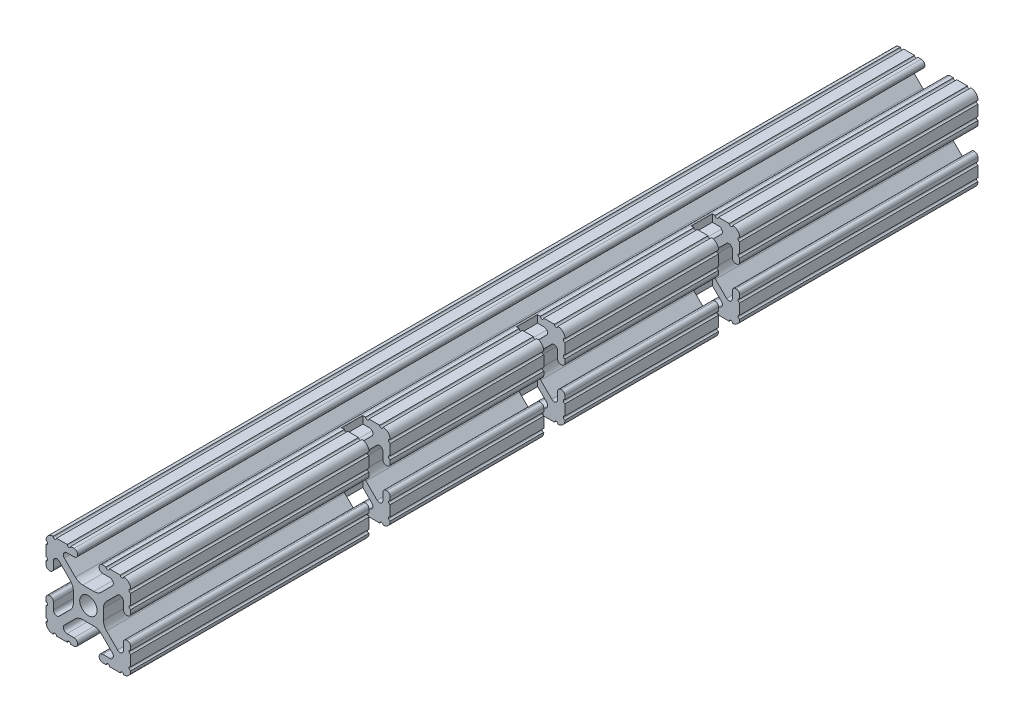
SolidWorks part; units mm, degrees
material "6061-T6 (SS)"
ref_plane "Front" through (0, 0, 0) normal (0, 0, 1) x (1, 0, 0)
ref_plane "Top" through (0, 0, 0) normal (0, 1, 0) x (1, 0, 0)
ref_plane "Right" through (0, 0, 0) normal (1, 0, 0) x (0, 0, -1)
sketch "Sketch1" plane through (0, 0, 0) normal (0, 0, 1) x (1, 0, 0)
  line L0 (-7.5107, 9.4563) -> (7.5107, 9.4563) construction
  line L1 (-7.4968, -9.4098) -> (7.4968, -9.4098) construction
  line L88 (-7.1797, -8.6452) -> (-3.9523, -5.4237)
  line L89 (-1.7093, -4.4958) -> (1.7093, -4.4958)
  line L90 (3.9523, -5.4237) -> (7.1797, -8.6452)
  line L91 (6.4164, -10.4902) -> (4.2875, -10.4902)
  line L92 (3.2385, -11.5392) -> (3.2385, -11.651)
  line L93 (4.2875, -12.7) -> (5.3171, -12.7)
  line L94 (6.3331, -12.7) -> (9.5504, -12.7)
  line L95 (12.7, -9.5504) -> (12.7, -6.3331)
  line L96 (12.7, -5.3171) -> (12.7, -4.2875)
  line L97 (11.651, -3.2385) -> (11.5392, -3.2385)
  line L98 (10.4902, -4.2875) -> (10.4902, -6.4021)
  line L99 (8.7371, -7.1294) -> (5.441, -3.8408)
  line L100 (4.5085, -1.5932) -> (4.5085, 1.5932)
  line L101 (5.441, 3.8408) -> (8.7371, 7.1294)
  line L102 (10.4902, 6.4021) -> (10.4902, 4.2875)
  line L103 (11.5392, 3.2385) -> (11.651, 3.2385)
  line L104 (12.7, 4.2875) -> (12.7, 5.3171)
  line L105 (12.7, 6.3331) -> (12.7, 9.5504)
  line L106 (9.5504, 12.7) -> (6.3331, 12.7)
  line L107 (5.3171, 12.7) -> (4.2875, 12.7)
  line L108 (3.2385, 11.651) -> (3.2385, 11.5392)
  line L109 (4.2875, 10.4902) -> (6.4768, 10.4902)
  line L110 (7.207, 8.7244) -> (3.8983, 5.4232)
  line L111 (1.6558, 4.4958) -> (-1.6558, 4.4958)
  line L112 (-3.8983, 5.4232) -> (-7.207, 8.7244)
  line L113 (-6.4768, 10.4902) -> (-4.2875, 10.4902)
  line L114 (-3.2385, 11.5392) -> (-3.2385, 11.651)
  line L115 (-4.2875, 12.7) -> (-5.3171, 12.7)
  line L116 (-6.3331, 12.7) -> (-9.5504, 12.7)
  line L117 (-12.7, 9.5504) -> (-12.7, 6.3331)
  line L118 (-12.7, 5.3171) -> (-12.7, 4.2875)
  line L119 (-11.651, 3.2385) -> (-11.5392, 3.2385)
  line L120 (-10.4902, 4.2875) -> (-10.4902, 6.4021)
  line L121 (-8.7371, 7.1294) -> (-5.441, 3.8408)
  line L122 (-4.5085, 1.5932) -> (-4.5085, -1.5932)
  line L123 (-5.441, -3.8408) -> (-8.7371, -7.1294)
  line L124 (-10.4902, -6.4021) -> (-10.4902, -4.2875)
  line L125 (-11.5392, -3.2385) -> (-11.651, -3.2385)
  line L126 (-12.7, -4.2875) -> (-12.7, -5.3171)
  line L127 (-12.7, -6.3331) -> (-12.7, -9.5504)
  line L128 (-9.5504, -12.7) -> (-6.3331, -12.7)
  line L129 (-5.3171, -12.7) -> (-4.2875, -12.7)
  line L130 (-3.2385, -11.651) -> (-3.2385, -11.5392)
  line L131 (-4.2875, -10.4902) -> (-6.4164, -10.4902)
  circle A1 centre (0, 0) radius 2.6035
  arc A104 (-7.1797, -8.6452) -> (-6.4164, -10.4902) centre (-6.4164, -9.4098) ccw
  arc A105 (-1.7093, -4.4958) -> (-3.9523, -5.4237) centre (-1.7093, -7.6708) ccw
  arc A106 (3.9523, -5.4237) -> (1.7093, -4.4958) centre (1.7093, -7.6708) ccw
  arc A107 (6.4164, -10.4902) -> (7.1797, -8.6452) centre (6.4164, -9.4098) ccw
  arc A108 (4.2875, -10.4902) -> (3.2385, -11.5392) centre (4.2875, -11.5392) ccw
  arc A109 (3.2385, -11.651) -> (4.2875, -12.7) centre (4.2875, -11.651) ccw
  arc A110 (6.3331, -12.7) -> (5.3171, -12.7) centre (5.8251, -12.7) ccw
  arc A111 (10.5664, -12.6998) -> (9.5504, -12.7) centre (10.0584, -12.7) ccw
  arc A112 (10.5664, -12.6998) -> (12.6998, -10.5664) centre (10.5918, -10.5918) ccw
  arc A113 (12.7, -9.5504) -> (12.6998, -10.5664) centre (12.7, -10.0584) ccw
  arc A114 (12.7, -5.3171) -> (12.7, -6.3331) centre (12.7, -5.8251) ccw
  arc A115 (12.7, -4.2875) -> (11.651, -3.2385) centre (11.651, -4.2875) ccw
  arc A116 (11.5392, -3.2385) -> (10.4902, -4.2875) centre (11.5392, -4.2875) ccw
  arc A117 (8.7371, -7.1294) -> (10.4902, -6.4021) centre (9.4628, -6.4021) ccw
  arc A118 (4.5085, -1.5932) -> (5.441, -3.8408) centre (7.6835, -1.5932) ccw
  arc A119 (5.441, 3.8408) -> (4.5085, 1.5932) centre (7.6835, 1.5932) ccw
  arc A120 (10.4902, 6.4021) -> (8.7371, 7.1294) centre (9.4628, 6.4021) ccw
  arc A121 (10.4902, 4.2875) -> (11.5392, 3.2385) centre (11.5392, 4.2875) ccw
  arc A122 (11.651, 3.2385) -> (12.7, 4.2875) centre (11.651, 4.2875) ccw
  arc A123 (12.7, 6.3331) -> (12.7, 5.3171) centre (12.7, 5.8251) ccw
  arc A124 (12.6998, 10.5664) -> (12.7, 9.5504) centre (12.7, 10.0584) ccw
  arc A125 (12.6998, 10.5664) -> (10.5664, 12.6998) centre (10.5918, 10.5918) ccw
  arc A126 (9.5504, 12.7) -> (10.5664, 12.6998) centre (10.0584, 12.7) ccw
  arc A127 (5.3171, 12.7) -> (6.3331, 12.7) centre (5.8251, 12.7) ccw
  arc A128 (4.2875, 12.7) -> (3.2385, 11.651) centre (4.2875, 11.651) ccw
  arc A129 (3.2385, 11.5392) -> (4.2875, 10.4902) centre (4.2875, 11.5392) ccw
  arc A130 (7.207, 8.7244) -> (6.4768, 10.4902) centre (6.4768, 9.4563) ccw
  arc A131 (1.6558, 4.4958) -> (3.8983, 5.4232) centre (1.6558, 7.6708) ccw
  arc A132 (-3.8983, 5.4232) -> (-1.6558, 4.4958) centre (-1.6558, 7.6708) ccw
  arc A133 (-6.4768, 10.4902) -> (-7.207, 8.7244) centre (-6.4768, 9.4563) ccw
  arc A134 (-4.2875, 10.4902) -> (-3.2385, 11.5392) centre (-4.2875, 11.5392) ccw
  arc A135 (-3.2385, 11.651) -> (-4.2875, 12.7) centre (-4.2875, 11.651) ccw
  arc A136 (-6.3331, 12.7) -> (-5.3171, 12.7) centre (-5.8251, 12.7) ccw
  arc A137 (-10.5664, 12.6998) -> (-9.5504, 12.7) centre (-10.0584, 12.7) ccw
  arc A138 (-10.5664, 12.6998) -> (-12.6998, 10.5664) centre (-10.5918, 10.5918) ccw
  arc A139 (-12.7, 9.5504) -> (-12.6998, 10.5664) centre (-12.7, 10.0584) ccw
  arc A140 (-12.7, 5.3171) -> (-12.7, 6.3331) centre (-12.7, 5.8251) ccw
  arc A141 (-12.7, 4.2875) -> (-11.651, 3.2385) centre (-11.651, 4.2875) ccw
  arc A142 (-11.5392, 3.2385) -> (-10.4902, 4.2875) centre (-11.5392, 4.2875) ccw
  arc A143 (-8.7371, 7.1294) -> (-10.4902, 6.4021) centre (-9.4628, 6.4021) ccw
  arc A144 (-4.5085, 1.5932) -> (-5.441, 3.8408) centre (-7.6835, 1.5932) ccw
  arc A145 (-5.441, -3.8408) -> (-4.5085, -1.5932) centre (-7.6835, -1.5932) ccw
  arc A146 (-10.4902, -6.4021) -> (-8.7371, -7.1294) centre (-9.4628, -6.4021) ccw
  arc A147 (-10.4902, -4.2875) -> (-11.5392, -3.2385) centre (-11.5392, -4.2875) ccw
  arc A148 (-11.651, -3.2385) -> (-12.7, -4.2875) centre (-11.651, -4.2875) ccw
  arc A149 (-12.7, -6.3331) -> (-12.7, -5.3171) centre (-12.7, -5.8251) ccw
  arc A150 (-12.6998, -10.5664) -> (-12.7, -9.5504) centre (-12.7, -10.0584) ccw
  arc A151 (-12.6998, -10.5664) -> (-10.5664, -12.6998) centre (-10.5918, -10.5918) ccw
  arc A152 (-9.5504, -12.7) -> (-10.5664, -12.6998) centre (-10.0584, -12.7) ccw
  arc A153 (-5.3171, -12.7) -> (-6.3331, -12.7) centre (-5.8251, -12.7) ccw
  arc A154 (-4.2875, -12.7) -> (-3.2385, -11.651) centre (-4.2875, -11.651) ccw
  arc A155 (-3.2385, -11.5392) -> (-4.2875, -10.4902) centre (-4.2875, -11.5392) ccw
extrude "Boss-Extrude1" add sketch "Sketch1" along normal mid plane 254
sketch "Sketch2" [suppressed] plane through (4.5085, 0, 0) normal (1, 0, 0) x (0, 0, -1)
  line L0 (-118.999, 0) -> (118.999, 0) construction
  line L1 (-118.999, 3.175) -> (118.999, 3.175)
  line L2 (-118.999, -3.175) -> (118.999, -3.175)
  line L3 (138.049, -1.5932) -> (138.049, 1.5932) construction
  arc A0 (-118.999, 3.175) -> (-118.999, -3.175) centre (-118.999, 0) ccw
  arc A1 (118.999, -3.175) -> (118.999, 3.175) centre (118.999, 0) ccw
  point P2 (0, 0)
  dimension "D2" = 3.175
  dimension "D1" = 12.7
extrude "Cut-Extrude1" [suppressed] cut sketch "Sketch2" against normal through all both and the other way through all
sketch "Sketch3" plane through (0, 12.7, 0) normal (0, 1, 0) x (1, 0, 0)
  line L0 (10.5664, -127) -> (10.5664, 127) construction
  line L1 (4.5085, 3.175) -> (16.6244, 3.175)
  line L2 (4.5085, 3.175) -> (4.5085, -3.175)
  line L3 (4.5085, -3.175) -> (16.6244, -3.175)
  line L4 (16.6244, 3.175) -> (16.6244, -3.175)
  line L5 (4.5085, 3.175) -> (16.6244, -3.175) construction
  line L6 (4.5085, -3.175) -> (16.6244, 3.175) construction
  line L7 (4.5085, -127) -> (4.5085, 127) construction
  line L8 (-16.6486, 0) -> (49.5946, 0) construction
  line L9 (4.5085, 55.5625) -> (16.6244, 55.5625)
  line L10 (4.5085, 55.5625) -> (4.5085, 49.2125)
  line L11 (4.5085, 49.2125) -> (16.6244, 49.2125)
  line L12 (16.6244, 55.5625) -> (16.6244, 49.2125)
  line L13 (4.5085, 55.5625) -> (16.6244, 49.2125) construction
  line L14 (4.5085, 49.2125) -> (16.6244, 55.5625) construction
  line L15 (4.5085, -49.2125) -> (16.6244, -55.5625) construction
  line L16 (4.5085, -55.5625) -> (16.6244, -49.2125) construction
  line L17 (16.6244, -55.5625) -> (16.6244, -49.2125)
  line L18 (4.5085, -49.2125) -> (16.6244, -49.2125)
  line L19 (4.5085, -55.5625) -> (4.5085, -49.2125)
  line L20 (4.5085, -55.5625) -> (16.6244, -55.5625)
  point P0 (10.5664, 0)
  point P9 (10.5664, 52.3875)
  point P21 (10.5664, -52.3875)
  dimension "D1" = 6.35
  dimension "D2" = 46.0375
extrude "Cut-Extrude2" cut sketch "Sketch3" against normal through all both and the other way through all
sketch "Sketch4" [suppressed] plane through (12.7, 0, 0) normal (1, 0, 0) x (0, 0, -1)
  line L0 (130.81, 12.6998) -> (51.6061, -33.0285)
  line L2 (51.6061, -33.0285) -> (130.81, -33.0285)
  line L3 (130.81, -33.0285) -> (130.81, 12.6998)
  dimension "D1" = 60
extrude "Cut-Extrude3" [suppressed] cut sketch "Sketch4" against normal through all both and the other way through all
